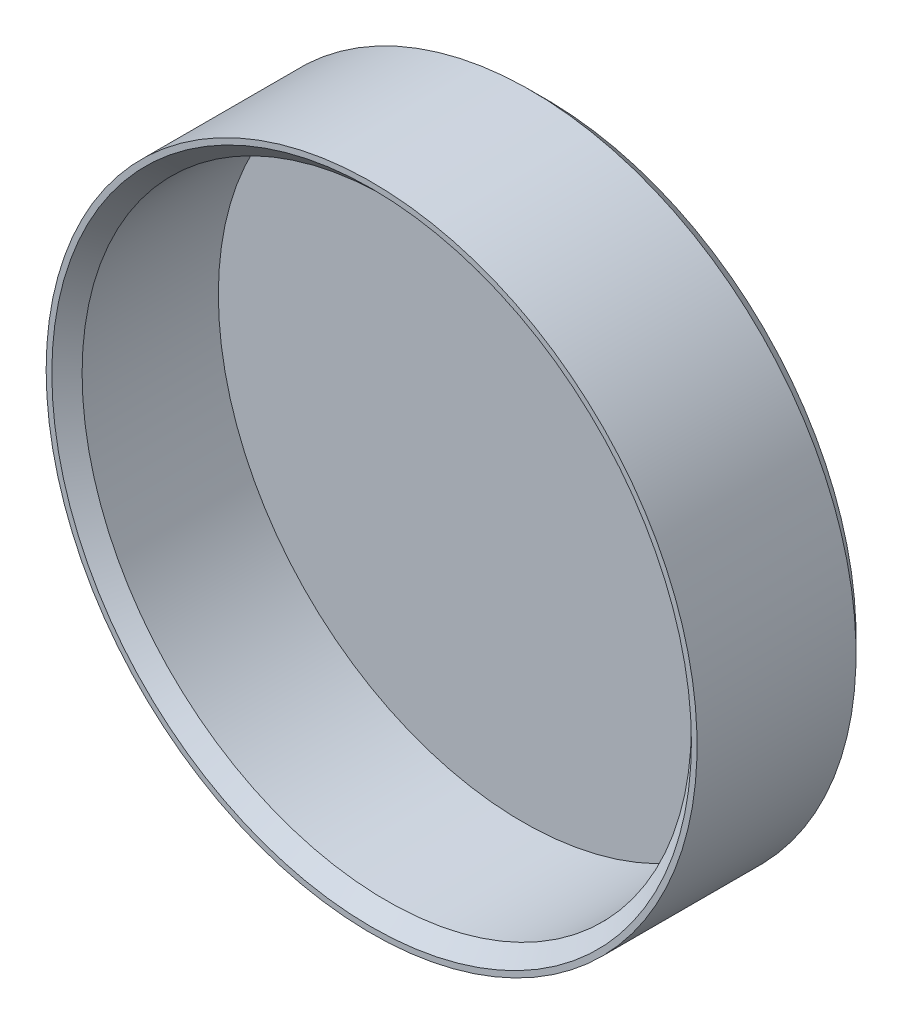
SolidWorks part; units mm, degrees
ref_plane "Plan de face" through (0, 0, 0) normal (0, 0, 1) x (1, 0, 0)
ref_plane "Plan de dessus" through (0, 0, 0) normal (0, 1, 0) x (1, 0, 0)
ref_plane "Plan de droite" through (0, 0, 0) normal (1, 0, 0) x (0, 0, -1)
sketch "Esquisse1" plane through (0, 0, 0) normal (1, 0, 0) x (0, 0, -1)
  line L0 (0, 0) -> (0, 40.25)
  line L1 (0, 40.25) -> (-18, 40.25)
  line L2 (-20, 42.25) -> (-20, 43)
  line L3 (-20, 43) -> (1, 43)
  line L4 (3, 41) -> (3, 0)
  line L5 (3, 0) -> (0, 0)
  line L7 (1, 43) -> (3, 41)
  line L8 (-18, 40.25) -> (-20, 42.25)
  point P3 (1.5, 0)
  point P6 (3, 43)
  point P8 (0, 0)
  point P9 (0, 0)
  point P10 (-20, 40.25)
  point P13 (-20, 40.25)
  point P14 (-18, 40.25)
  point P15 (-18, 40.25)
  point P16 (-20.9017, 40.25)
  dimension "D1" = 3
  dimension "D2" = 40.25
  dimension "D3" = 43
  dimension "D4" = 20
revolve "Révolution1" add sketch "Esquisse1" angle 360 about L5
